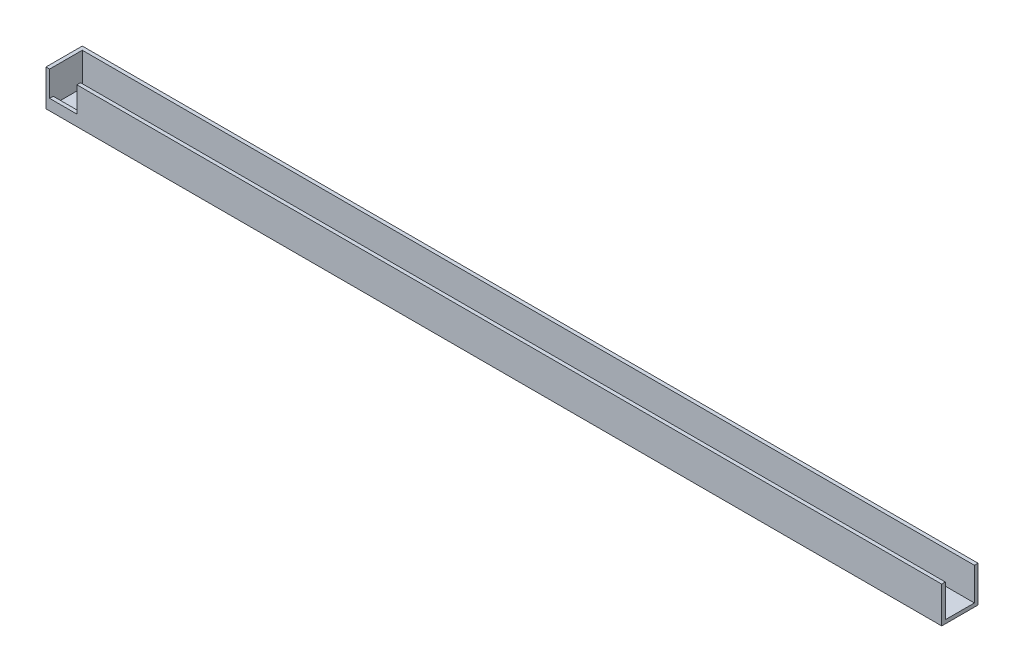
SolidWorks part; units mm, degrees
ref_plane "Front Plane" through (0, 0, 0) normal (0, 0, 1) x (1, 0, 0)
ref_plane "Top Plane" through (0, 0, 0) normal (0, 1, 0) x (1, 0, 0)
ref_plane "Right Plane" through (0, 0, 0) normal (1, 0, 0) x (0, 0, -1)
sketch "Sketch1" plane through (0, 0, 0) normal (0, 0, 1) x (1, 0, 0)
  line L0 (-784.225, 0) -> (784.225, 0)
  line L1 (-784.225, 0) -> (-784.225, 63.5)
  line L2 (-784.225, 63.5) -> (784.225, 63.5)
  line L3 (784.225, 63.5) -> (784.225, 0)
  point P4 (0, 0)
  dimension "D1" = 1568.45
  dimension "D2" = 63.5
extrude "Boss-Extrude1" add sketch "Sketch1" along normal blind 63.5
shell "Shell1" thickness 6.35
sketch "Sketch3" plane through (0, 0, 63.5) normal (0, 0, 1) x (1, 0, 0)
  line L7 (-777.875, 63.5) -> (-730.123, 63.5)
  line L8 (-777.875, 63.5) -> (-777.875, 19.05)
  line L9 (-777.875, 19.05) -> (-730.123, 19.05)
  line L10 (-730.123, 63.5) -> (-730.123, 19.05)
  dimension "D1" = 44.45
  dimension "D2" = 47.752
extrude "Cut-Extrude1" cut sketch "Sketch3" against normal up to surface (6.35 mm away) up to face at (3.175, 34.925, 57.15)
equation "\"in7.29794934in\"=7.29795"
